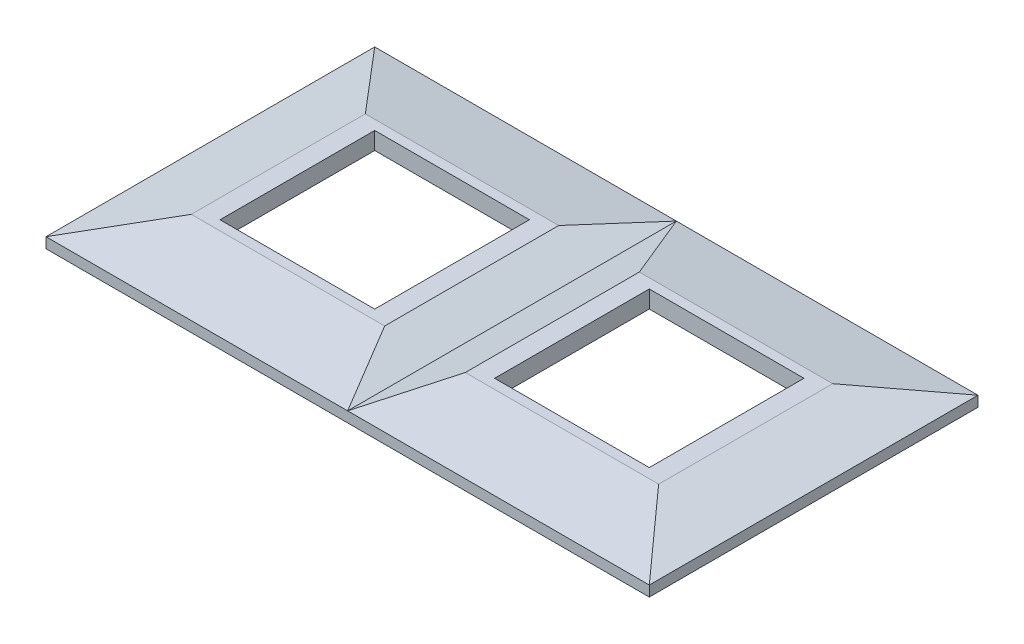
SolidWorks part; units mm, degrees
ref_plane "Спереди" through (0, 0, 0) normal (0, 0, 1) x (1, 0, 0)
ref_plane "Сверху" through (0, 0, 0) normal (0, 1, 0) x (1, 0, 0)
ref_plane "Справа" through (0, 0, 0) normal (1, 0, 0) x (0, 0, -1)
sketch "Эскиз1" plane through (0, 0, 0) normal (0, 0, 1) x (1, 0, 0)
  line L0 (0, 0) -> (-78, 0)
  line L1 (-78, 0) -> (-78, 2.7052)
  line L2 (-78, 2.7052) -> (-60.4232, 6.5)
  line L3 (-60.4232, 6.5) -> (-10.4232, 6.5)
  line L5 (0, 2.7052) -> (-10.4232, 6.5)
  line L6 (0, 40.9923) -> (0, -28.3407) construction
  line L7 (0, 2.7052) -> (10.4232, 6.5)
  line L8 (0, 0) -> (78, 0)
  line L9 (60.4232, 6.5) -> (10.4232, 6.5)
  line L10 (78, 2.7052) -> (60.4232, 6.5)
  line L11 (78, 0) -> (78, 2.7052)
  point P7 (-39, 0)
  point P8 (-35.4232, 6.5)
  point P14 (35.4232, 6.5)
  point P15 (39, 0)
  point P16 (0, 0)
  point P17 (0, 0)
  point P18 (0, 0)
  point P19 (0, 0)
extrude "Бобышка-Вытянуть1" add sketch "Эскиз1" along normal mid plane 85
sketch "Эскиз2" plane through (0, 0, 0) normal (1, 0, 0) x (0, 0, -1)
  line L0 (42.5, 0) -> (-42.5, 0)
  line L1 (-42.5, 2.7052) -> (-22.5, 6.5)
  line L2 (-42.5, 6.5) -> (42.5, 6.5) construction
  line L3 (-22.5, 6.5) -> (22.5, 6.5)
  line L5 (-42.5, 0) -> (-42.5, 2.7052)
  line L6 (0, 24.25) -> (0, -8.715) construction
  line L7 (42.5, 0) -> (42.5, 2.7052)
  line L8 (42.5, 2.7052) -> (22.5, 6.5)
  point P12 (0, 0)
  point P13 (0, 6.5)
  point P15 (0, 0)
  point P17 (0, 6.5)
extrude "Вырез-Вытянуть1" cut sketch "Эскиз2" against normal mid plane 156 flip side to cut
sketch "Эскиз3" plane through (0, 0, 0) normal (0, -1, 0) x (1, 0, 0)
  line L0 (0, 44.7636) -> (0, -49.792) construction
  line L1 (-55.5, 20) -> (-15.5, 20)
  line L2 (-55.5, 20) -> (-55.5, -20)
  line L3 (-55.5, -20) -> (-15.5, -20)
  line L4 (-15.5, 20) -> (-15.5, -20)
  line L5 (-55.5, 20) -> (-15.5, -20) construction
  line L6 (-55.5, -20) -> (-15.5, 20) construction
  line L7 (55.5, -20) -> (15.5, 20) construction
  line L8 (55.5, 20) -> (15.5, -20) construction
  line L9 (15.5, 20) -> (15.5, -20)
  line L10 (55.5, -20) -> (15.5, -20)
  line L11 (55.5, 20) -> (55.5, -20)
  line L12 (55.5, 20) -> (15.5, 20)
  point P0 (-35.5, 0)
  point P12 (35.5, 0)
  point P13 (0, 0)
extrude "Вырез-Вытянуть2" cut sketch "Эскиз3" against normal through all
sketch "Эскиз4" plane through (0, 0, 0) normal (0, -1, 0) x (1, 0, 0)
  line L0 (0, 52.3062) -> (0, -49.5733) construction
  line L6 (-76, 41) -> (76, 41)
  line L7 (-76, 41) -> (-76, -41)
  line L8 (-76, -41) -> (76, -41)
  line L13 (76, 41) -> (76, -41)
  line L14 (-76, 41) -> (76, -41) construction
  line L15 (-76, -41) -> (76, 41) construction
  point P0 (-35.5, 0)
  point P1 (0, 0)
  point P12 (35.5, 0)
extrude "Вырез-Вытянуть3" cut sketch "Эскиз4" against normal blind 2
